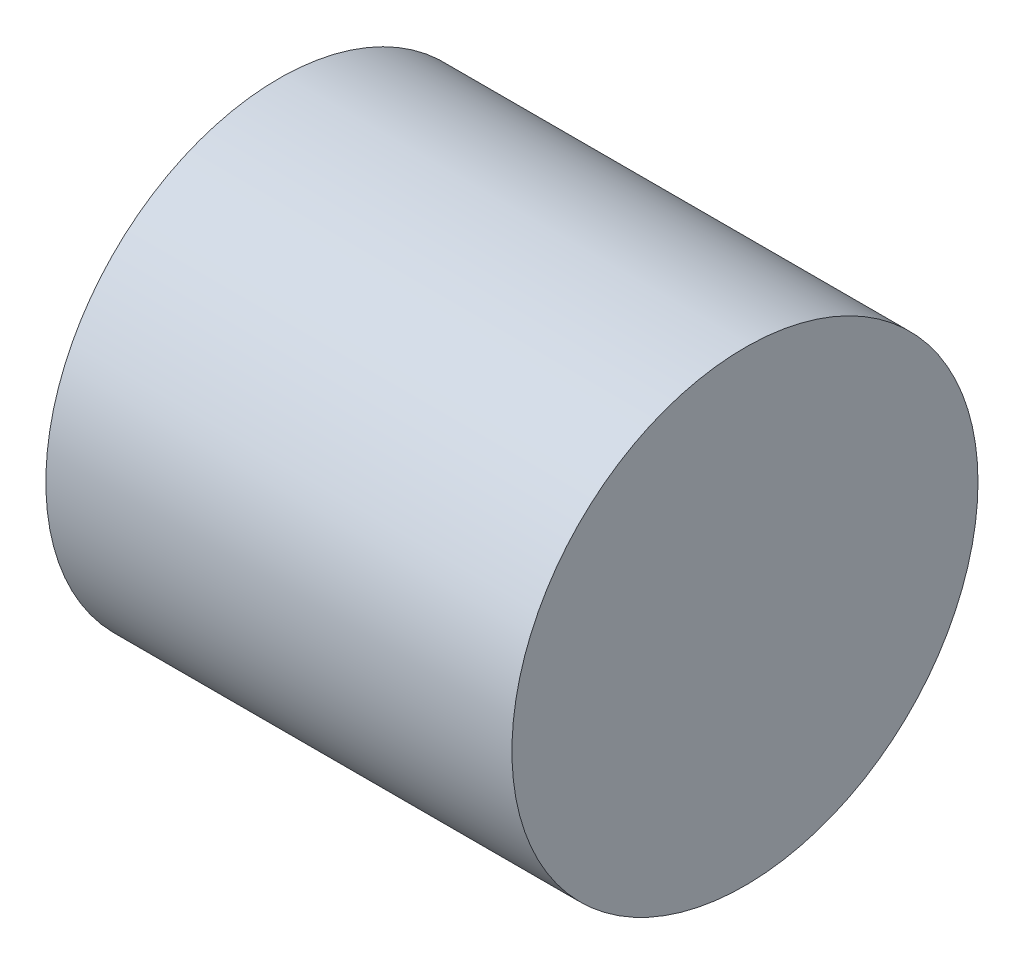
SolidWorks part; units mm, degrees
ref_plane "Front Plane" through (0, 0, 0) normal (0, 0, 1) x (1, 0, 0)
ref_plane "Top Plane" through (0, 0, 0) normal (0, 1, 0) x (1, 0, 0)
ref_plane "Right Plane" through (0, 0, 0) normal (1, 0, 0) x (0, 0, -1)
sketch "Sketch1" plane through (0, 0, 0) normal (1, 0, 0) x (0, 0, -1)
  circle A0 centre (-77.0947, 47.4526) radius 9.525
  dimension "D1" = 19.05
extrude "Extrude1" add sketch "Sketch1" along normal blind 19.05
